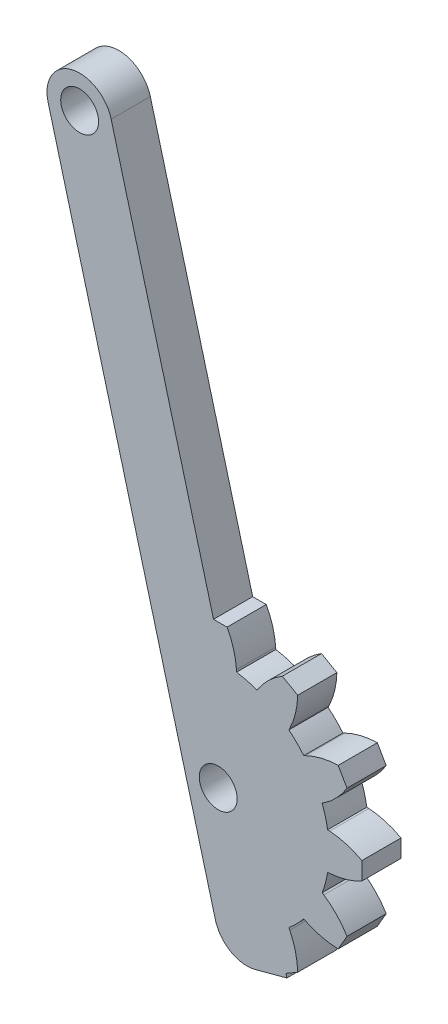
SolidWorks part; units mm, degrees
ref_plane "Front Plane" through (0, 0, 0) normal (0, 0, 1) x (1, 0, 0)
ref_plane "Top Plane" through (0, 0, 0) normal (0, 1, 0) x (1, 0, 0)
ref_plane "Right Plane" through (0, 0, 0) normal (1, 0, 0) x (0, 0, -1)
ref_plane "Plane1" through (0, 0, 1.9) normal (0, 0, 1) x (1, 0, 0)
sketch "Sketch1" plane through (0, 0, 1.9) normal (0, 0, 1) x (1, 0, 0)
  line L0 (-13.0264, 38.9559) -> (-0.2149, -8.8574)
  line L1 (2.847, -10.6252) -> (5.2618, -9.9781)
  line L2 (5.2618, -9.9781) -> (5.1889, -9.7059)
  line L3 (5.1889, -9.7059) -> (6.0876, -9.187)
  line L4 (5.4819, -6.6916) -> (5.4141, -6.5527)
  line L5 (6.5527, -5.4141) -> (6.6916, -5.4819)
  line L6 (9.187, -6.0876) -> (9.8655, -4.9124)
  line L7 (8.0933, -3.0542) -> (7.9651, -2.9677)
  line L8 (8.3818, -1.4124) -> (8.5361, -1.4016)
  line L9 (11, -0.6785) -> (11, 0.6785)
  line L10 (8.5361, 1.4016) -> (8.3818, 1.4124)
  line L11 (7.9651, 2.9677) -> (8.0933, 3.0542)
  line L12 (9.8655, 4.9124) -> (9.187, 6.0876)
  line L13 (6.6916, 5.4819) -> (6.5527, 5.4141)
  line L14 (5.4141, 6.5527) -> (5.4819, 6.6916)
  line L15 (6.0876, 9.187) -> (4.9124, 9.8655)
  line L16 (3.0542, 8.0933) -> (2.9677, 7.9651)
  line L17 (1.4124, 8.3818) -> (1.4016, 8.5361)
  line L18 (0.6785, 11) -> (-0.3593, 11)
  line L19 (-0.3593, 11) -> (-8.1968, 40.25)
  line L20 (0, 0) -> (-10.6116, 39.603) construction
  circle A0 centre (-10.6116, 39.603) radius 1.45
  arc A1 (-0.2149, -8.8574) -> (2.847, -10.6252) centre (2.2, -8.2104) ccw
  arc A2 (6.0876, -9.187) -> (5.4819, -6.6916) centre (0.0891, -9.3218) ccw
  arc A3 (5.4141, -6.5527) -> (6.5527, -5.4141) centre (0, 0) ccw
  arc A4 (6.6916, -5.4819) -> (9.187, -6.0876) centre (9.3218, -0.0891) ccw
  arc A5 (9.8655, -4.9124) -> (8.0933, -3.0542) centre (4.7381, -8.0284) ccw
  arc A6 (7.9651, -2.9677) -> (8.3818, -1.4124) centre (0, 0) ccw
  arc A7 (8.5361, -1.4016) -> (11, -0.6785) centre (8.1175, 4.5837) ccw
  arc A8 (11, 0.6785) -> (8.5361, 1.4016) centre (8.1175, -4.5837) ccw
  arc A9 (8.3818, 1.4124) -> (7.9651, 2.9677) centre (0, 0) ccw
  arc A10 (8.0933, 3.0542) -> (9.8655, 4.9124) centre (4.7381, 8.0284) ccw
  arc A11 (9.187, 6.0876) -> (6.6916, 5.4819) centre (9.3218, 0.0891) ccw
  arc A12 (6.5527, 5.4141) -> (5.4141, 6.5527) centre (0, 0) ccw
  arc A13 (5.4819, 6.6916) -> (6.0876, 9.187) centre (0.0891, 9.3218) ccw
  arc A14 (4.9124, 9.8655) -> (3.0542, 8.0933) centre (8.0284, 4.7381) ccw
  arc A15 (2.9677, 7.9651) -> (1.4124, 8.3818) centre (0, 0) ccw
  arc A16 (1.4016, 8.5361) -> (0.6785, 11) centre (-4.5837, 8.1175) ccw
  arc A17 (-8.1968, 40.25) -> (-13.0264, 38.9559) centre (-10.6116, 39.603) ccw
  circle A18 centre (0, 0) radius 1.45
  dimension "D1" = 2.9
  dimension "D3" = 0.0891
  dimension "D4" = 8.5
  dimension "D5" = 6
  dimension "D20" = 2.9
  dimension "D6" = 0.6785
  dimension "D7" = 1.4016
  dimension "D8" = 1.4124
  dimension "D9" = 2.2
  dimension "D10" = 2.847
  dimension "D11" = 2.9677
  dimension "D12" = 3.0542
  dimension "D13" = 4.7381
  dimension "D14" = 4.9124
  dimension "D15" = 5.1889
  dimension "D16" = 5.4141
  dimension "D17" = 6.5527
  dimension "D18" = 8.1175
  dimension "39" = 41
extrude "Boss-Extrude1" add sketch "Sketch1" against normal blind 3
